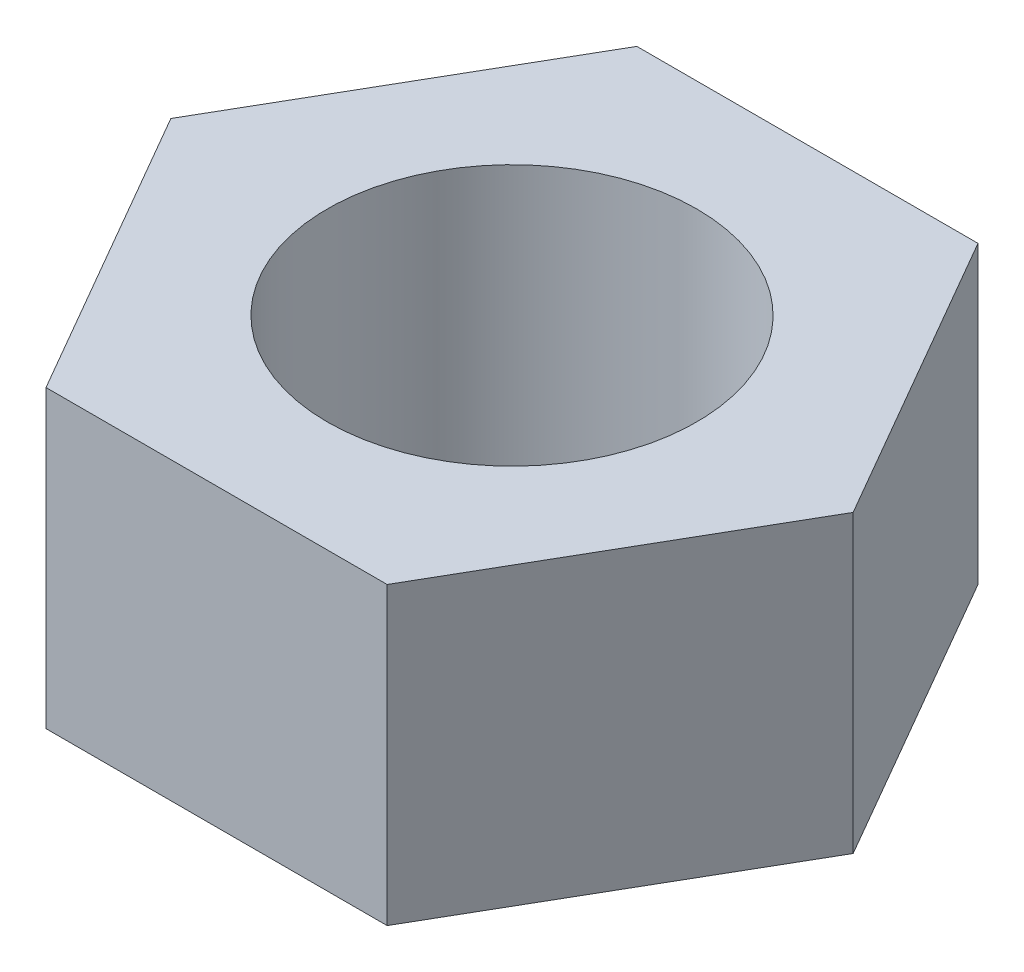
SolidWorks part; units mm, degrees
ref_plane "Front" through (0, 0, 0) normal (0, 0, 1) x (1, 0, 0)
ref_plane "Top" through (0, 0, 0) normal (0, 1, 0) x (1, 0, 0)
ref_plane "Right" through (0, 0, 0) normal (1, 0, 0) x (0, 0, -1)
sketch "Sketch1" plane through (0, 0, 0) normal (0, 1, 0) x (1, 0, 0)
  line L1 (-4.6188, 0) -> (-2.3094, -4)
  line L2 (-2.3094, -4) -> (2.3094, -4)
  line L3 (2.3094, -4) -> (4.6188, 0)
  line L4 (4.6188, 0) -> (2.3094, 4)
  line L5 (2.3094, 4) -> (-2.3094, 4)
  line L6 (-2.3094, 4) -> (-4.6188, 0)
  circle A0 centre (0, 0) radius 2.5
  circle A1 centre (0, 0) radius 4 construction
  point P3 (0, 0)
  dimension "D1" = 5
  dimension "D2" = 8
extrude "Boss-Extrude1" add sketch "Sketch1" along normal blind 4
